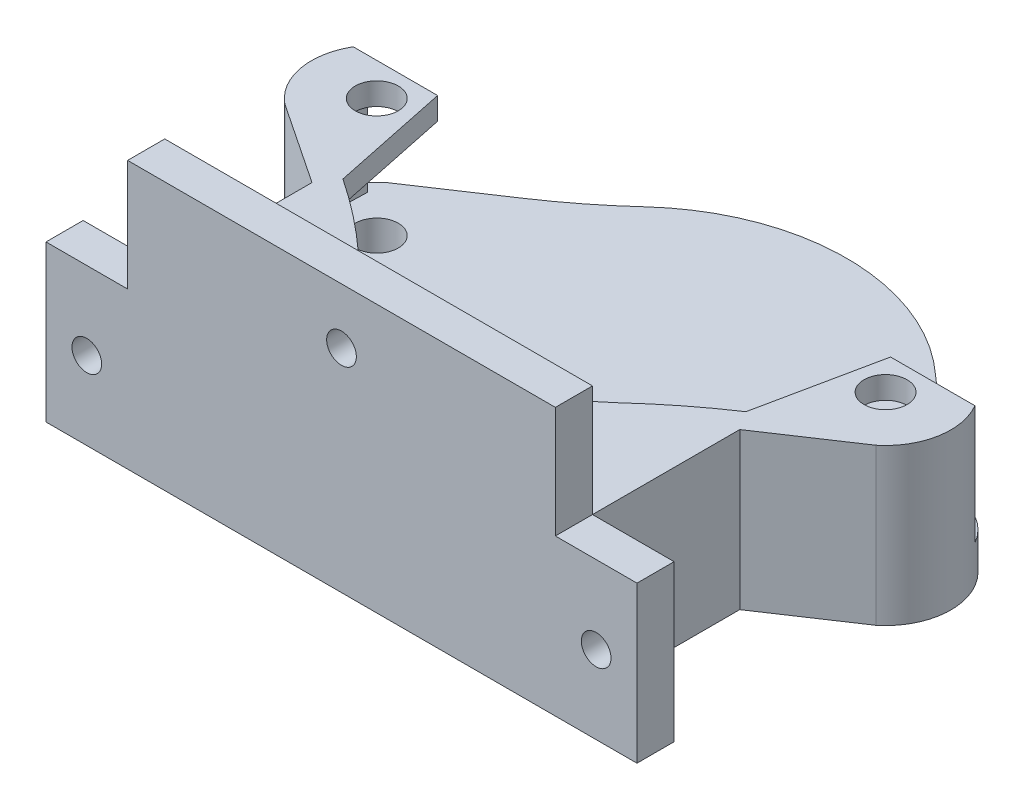
SolidWorks part; units mm, degrees
ref_plane "Front Plane" through (0, 0, 0) normal (0, 0, 1) x (1, 0, 0)
ref_plane "Top Plane" through (0, 0, 0) normal (0, 1, 0) x (1, 0, 0)
ref_plane "Right Plane" through (0, 0, 0) normal (1, 0, 0) x (0, 0, -1)
sketch "Sketch1" plane through (0, 0, 0) normal (0, 1, 0) x (1, 0, 0)
  line L0 (62.9004, 19.0691) -> (73.8872, 26.3996)
  line L6 (62.9004, 47.4193) -> (73.8872, 40.0888)
  line L7 (5.3122, 47.4193) -> (-5.6747, 40.0888)
  line L8 (5.3122, 19.0691) -> (-5.6747, 26.3996)
  circle A4 centre (68.3563, 33.2442) radius 2.9
  circle A9 centre (-0.1437, 33.2442) radius 2.9
  arc A12 (73.8872, 26.3996) -> (73.8872, 40.0888) centre (68.3563, 33.2442) ccw
  arc A13 (53.6758, 54.6459) -> (62.9004, 47.4193) centre (105.6362, 111.4712) ccw
  arc A14 (53.6758, 54.6459) -> (14.5367, 54.6459) centre (34.1063, 33.2442) ccw
  arc A15 (14.5367, 54.6459) -> (5.3122, 47.4193) centre (-37.4237, 111.4712) cw
  arc A16 (-5.6747, 26.3996) -> (-5.6747, 40.0888) centre (-0.1437, 33.2442) cw
  arc A17 (14.5367, 11.8425) -> (5.3122, 19.0691) centre (-37.4237, -44.9828) ccw
  arc A18 (14.5367, 11.8425) -> (53.6758, 11.8425) centre (34.1063, 33.2442) ccw
  arc A19 (53.6758, 11.8425) -> (62.9004, 19.0691) centre (105.6362, -44.9828) cw
extrude "Boss-Extrude1" add sketch "Sketch1" along normal blind 5
sketch "Sketch3" plane through (0, 5, 0) normal (0, 1, 0) x (1, 0, 0)
  line L0 (62.9004, 19.0691) -> (73.8872, 26.3996)
  line L1 (61.2354, 21.5647) -> (72.0964, 28.8112)
  line L2 (6.9772, 21.5647) -> (-3.8838, 28.8112)
  line L3 (5.3122, 19.0691) -> (-5.6747, 26.3996)
  line L4 (74.0272, 37.6772) -> (75.9581, 37.6772)
  line L5 (-5.8147, 37.6772) -> (-7.7456, 37.6772)
  line L6 (-5.9437, 33.2442) -> (-5.8147, 37.6772)
  line L8 (74.1563, 33.2442) -> (74.0272, 37.6772)
  arc A0 (16.5612, 14.0565) -> (51.6514, 14.0565) centre (34.1063, 33.2442) ccw
  arc A2 (72.0964, 28.8112) -> (74.1563, 33.2442) centre (68.3563, 33.2442) ccw
  arc A3 (51.6514, 14.0565) -> (61.2354, 21.5647) centre (105.6362, -44.9828) cw
  arc A4 (-3.8838, 28.8112) -> (-5.9437, 33.2442) centre (-0.1437, 33.2442) cw
  arc A6 (16.5612, 14.0565) -> (6.9772, 21.5647) centre (-37.4237, -44.9828) ccw
  arc A7 (73.8872, 26.3996) -> (75.9581, 37.6772) centre (68.3563, 33.2442) ccw
  arc A8 (-5.6747, 26.3996) -> (-7.7456, 37.6772) centre (-0.1437, 33.2442) cw
  arc A9 (14.5367, 11.8425) -> (5.3122, 19.0691) centre (-37.4237, -44.9828) ccw
  arc A10 (14.5367, 11.8425) -> (53.6758, 11.8425) centre (34.1063, 33.2442) ccw
  arc A11 (53.6758, 11.8425) -> (62.9004, 19.0691) centre (105.6362, -44.9828) cw
extrude "Boss-Extrude2" add sketch "Sketch3" along normal blind 13
sketch "Sketch4" plane through (0, 18, 0) normal (0, 1, 0) x (1, 0, 0)
  line L0 (3.6162, 37.6772) -> (-7.7456, 37.6772)
  line L1 (62.9004, 19.0691) -> (73.8872, 26.3996)
  line L4 (5.3122, 19.0691) -> (-5.6747, 26.3996)
  line L11 (3.6162, 37.6772) -> (6.9772, 21.5647)
  line L12 (64.5964, 37.6772) -> (61.2354, 21.5647)
  line L13 (64.5964, 37.6772) -> (75.9581, 37.6772)
  arc A3 (16.5612, 14.0565) -> (51.6514, 14.0565) centre (34.1063, 33.2442) ccw
  arc A6 (51.6514, 14.0565) -> (61.2354, 21.5647) centre (105.6362, -44.9828) cw
  arc A9 (16.5612, 14.0565) -> (6.9772, 21.5647) centre (-37.4237, -44.9828) ccw
  arc A10 (73.8872, 26.3996) -> (75.9581, 37.6772) centre (68.3563, 33.2442) ccw
  arc A11 (-5.6747, 26.3996) -> (-7.7456, 37.6772) centre (-0.1437, 33.2442) cw
  arc A12 (14.5367, 11.8425) -> (5.3122, 19.0691) centre (-37.4237, -44.9828) ccw
  arc A13 (14.5367, 11.8425) -> (53.6758, 11.8425) centre (34.1063, 33.2442) ccw
  arc A14 (53.6758, 11.8425) -> (62.9004, 19.0691) centre (105.6362, -44.9828) cw
  circle A15 centre (-0.1437, 33.2442) radius 2.9
  circle A16 centre (68.3563, 33.2442) radius 2.9
extrude "Boss-Extrude3" add sketch "Sketch4" along normal blind 3
sketch "Sketch5" plane through (0, 0, 0) normal (0, -1, 0) x (1, 0, 0)
  line L7 (62.9004, -19.0691) -> (62.9004, 5.7558)
  line L8 (62.9004, 5.7558) -> (5.3122, 5.7558)
  line L9 (5.3122, 5.7558) -> (5.3122, -19.0691)
  arc A15 (14.5367, -11.8425) -> (5.3122, -19.0691) centre (-37.4237, 44.9828) cw
  arc A17 (53.6758, -11.8425) -> (62.9004, -19.0691) centre (105.6362, 44.9828) ccw
  arc A19 (14.5367, -11.8425) -> (53.6758, -11.8425) centre (34.1063, -33.2442) cw
extrude "Boss-Extrude4" add sketch "Sketch5" against normal blind 21
sketch "Sketch7" plane through (0, 0, 5.7558) normal (0, 0, 1) x (1, 0, 0)
  line L0 (62.9004, 21) -> (5.3122, 21)
  line L1 (5.3122, 21) -> (5.3122, 36)
  line L2 (5.3122, 36) -> (62.9004, 36)
  line L3 (62.9004, 36) -> (62.9004, 21)
  line L4 (34.1063, 21) -> (34.1063, 36) construction
  circle A0 centre (34.1063, 28.5) radius 2
extrude "Boss-Extrude6" add sketch "Sketch7" against normal blind 5
sketch "Sketch9" plane through (0, 0, 5.7558) normal (0, 0, 1) x (1, 0, 0)
  line L0 (68.3938, 21) -> (68.3938, 0) construction
  line L1 (62.9004, 0) -> (73.8872, 0)
  line L2 (62.9004, 0) -> (62.9004, 21)
  line L3 (62.9004, 21) -> (73.8872, 21)
  line L4 (73.8872, 0) -> (73.8872, 21)
  line L5 (34.1063, 36) -> (34.1063, 31.6824) construction
  line L6 (62.9004, 36) -> (5.3122, 36) construction
  line L7 (-0.1813, 21) -> (-0.1813, 0) construction
  line L8 (-5.6747, 0) -> (-5.6747, 21)
  line L9 (5.3122, 21) -> (-5.6747, 21)
  line L10 (5.3122, 0) -> (5.3122, 21)
  line L11 (5.3122, 0) -> (-5.6747, 0)
  circle A0 centre (68.3938, 10.5) radius 2
  circle A1 centre (-0.1813, 10.5) radius 2
extrude "Boss-Extrude7" add sketch "Sketch9" against normal blind 5
